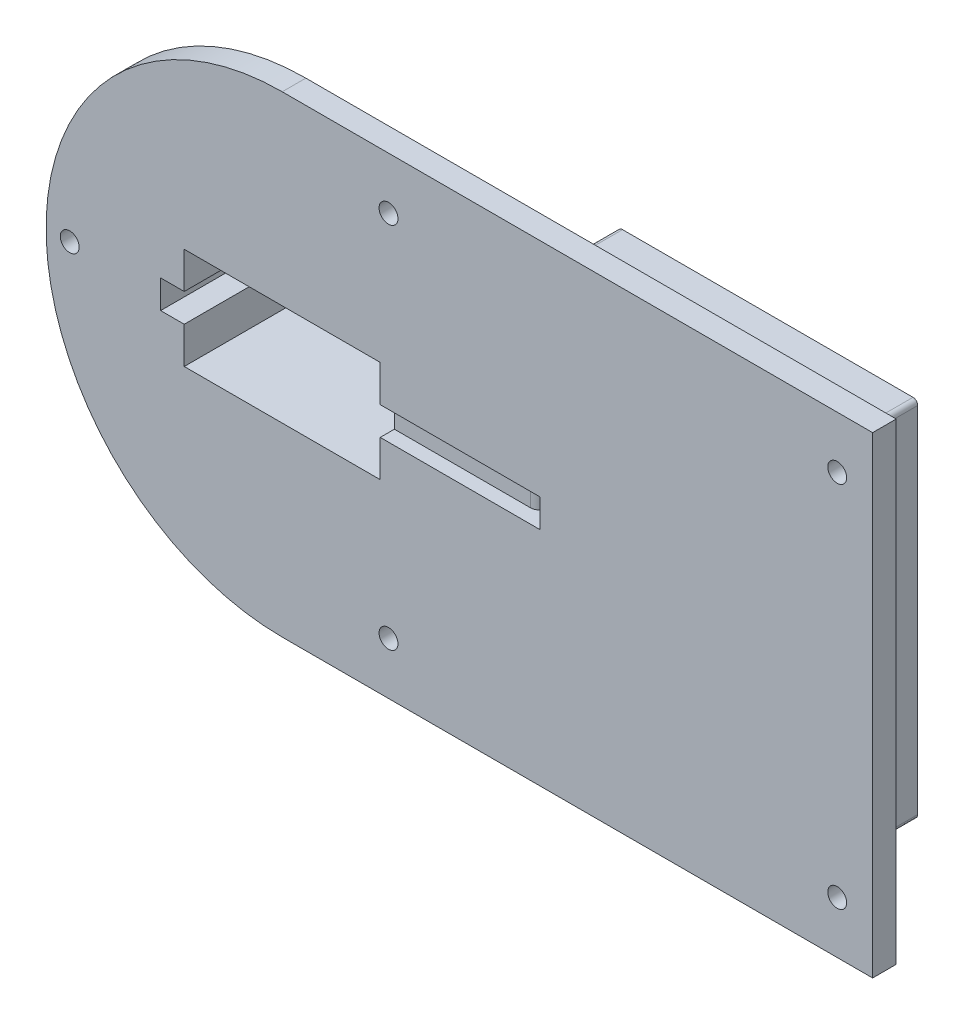
SolidWorks part; units mm, degrees
ref_plane "Front Plane" through (0, 0, 0) normal (0, 0, 1) x (1, 0, 0)
ref_plane "Top Plane" through (0, 0, 0) normal (0, 1, 0) x (1, 0, 0)
ref_plane "Right Plane" through (0, 0, 0) normal (1, 0, 0) x (0, 0, -1)
sketch "Sketch1" plane through (0, 0, 0) normal (0, 0, 1) x (1, 0, 0)
  line L1 (-20.75, 10.75) -> (20.75, 10.75)
  line L2 (-20.75, 10.75) -> (-20.75, -10.75)
  line L3 (-20.75, -10.75) -> (20.75, -10.75)
  line L4 (20.75, 10.75) -> (20.75, -10.75)
  line L5 (-20.75, 10.75) -> (20.75, -10.75) construction
  line L6 (-20.75, -10.75) -> (20.75, 10.75) construction
  line L11 (30, 15) -> (-30, 15)
  line L12 (30, 15) -> (30, -15)
  line L13 (30, -15) -> (-30, -15)
  line L14 (-30, 15) -> (-30, -15)
  line L15 (30, 15) -> (-30, -15) construction
  line L16 (30, -15) -> (-30, 15) construction
  point P0 (0, 0)
  point P6 (0, 0)
extrude "Boss-Extrude1" add sketch "Sketch1" along normal blind 27
sketch "Sketch2" plane through (0, 0, 27) normal (0, 0, 1) x (1, 0, 0)
  circle A0 centre (0, 0) radius 50
extrude "Boss-Extrude2" add sketch "Sketch2" along normal blind 5
fillet "Fillet2" radius 10 4 edges at (-30, 0, 27) (30, 0, 27) (0, 15, 27) (0, -15, 27)
sketch "Sketch6" plane through (0, 0, 0) normal (0, 0, -1) x (-1, 0, 0)
  line L0 (30, 5.975) -> (24.4, 5.975) construction
  line L1 (30, -15) -> (30, 15) construction
  line L2 (24.4, 15) -> (24.4, 5) construction
  line L3 (30, 15) -> (-30, 15) construction
  line L4 (0, 0) -> (11.2305, 0) construction
  line L5 (0, 0) -> (0, 9.663) construction
  circle A0 centre (24.4, 5) radius 1
  circle A1 centre (-24.4, 5) radius 1
  circle A2 centre (24.4, -5) radius 1
  circle A3 centre (-24.4, -5) radius 1
extrude "Cut-Extrude2" cut sketch "Sketch6" against normal blind 15
sketch "Sketch7" plane through (0, 0, 0) normal (0, 0, -1) x (-1, 0, 0)
  line L1 (-20.75, 10.75) -> (20.75, 10.75)
  line L2 (-20.75, 10.75) -> (-20.75, -10.75)
  line L3 (-20.75, -10.75) -> (20.75, -10.75)
  line L4 (20.75, 10.75) -> (20.75, -10.75)
  line L5 (-20.75, 10.75) -> (20.75, -10.75) construction
  line L6 (-20.75, -10.75) -> (20.75, 10.75) construction
  point P0 (0, 0)
extrude "Cut-Extrude3" cut sketch "Sketch7" against normal blind 69
sketch "Sketch8" plane through (0, 0, 0) normal (0, 0, -1) x (-1, 0, 0)
  line L0 (20.75, 10.75) -> (20.75, -10.75) construction
  line L1 (15.75, 3) -> (25.75, 3)
  line L2 (15.75, 3) -> (15.75, -3)
  line L3 (15.75, -3) -> (25.75, -3)
  line L4 (25.75, 3) -> (25.75, -3)
  line L5 (15.75, 3) -> (25.75, -3) construction
  line L6 (15.75, -3) -> (25.75, 3) construction
  point P0 (20.75, 0)
extrude "Cut-Extrude4" cut sketch "Sketch8" against normal blind 75
sketch "Sketch10" plane through (0, 0, 32) normal (0, 0, 1) x (1, 0, 0)
  line L0 (-25.75, 3) -> (-25.75, -3) construction
  line L1 (0, 3) -> (74.5949, 3)
  line L3 (0, -3) -> (74.5949, -3)
  line L4 (74.5949, 3) -> (74.5949, -3)
  line L5 (0, -0.7698) -> (74.5949, -3) construction
  line L6 (0, 0.7698) -> (74.5949, 3) construction
  line L7 (0, 3) -> (0, -3)
  point P0 (-25.75, 0)
extrude "Cut-Extrude5" cut sketch "Sketch10" against normal blind 3
sketch "Sketch11" plane through (0, 0, 27) normal (0, 0, -1) x (-1, 0, 0)
  line L0 (0, 0) -> (-45, 0) construction
  line L1 (0, 0) -> (45, 0) construction
  line L2 (0, 0) -> (-22.5, -38.9711) construction
  line L3 (0, 0) -> (-22.5, 38.9711) construction
  circle A3 centre (45, 0) radius 2
  circle A4 centre (-22.5, 38.9711) radius 2
  circle A5 centre (-22.5, -38.9711) radius 2
extrude "Cut-Extrude6" cut sketch "Sketch11" against normal blind 16
sketch "Sketch12" plane through (0, 0, 27) normal (0, 0, -1) x (-1, 0, 0)
  line L1 (0, -50) -> (-125, -50)
  line L3 (0, 50) -> (-125, 50)
  line L4 (-125, -50) -> (-125, 50)
  line L5 (-46.4238, 18.5695) -> (-125, 50) construction
  line L6 (-46.4238, -18.5695) -> (-125, -50) construction
  arc A0 (0, 50) -> (0, -50) centre (0, 0) ccw
  point P0 (0, 0)
extrude "Boss-Extrude3" add sketch "Sketch12" against normal up to surface (5 mm away) up to face at (-43, 0, 32)
sketch "Sketch13" plane through (0, 0, 27) normal (0, 0, -1) x (-1, 0, 0)
  line L0 (-99.6294, -50) -> (-99.6294, -20) construction
  line L1 (-125, -50) -> (0, -50) construction
  line L2 (-125, -20) -> (-104.5, -20) construction
  line L3 (-125, 50) -> (-125, -50) construction
  circle A0 centre (-104.5, -20) radius 1
  circle A1 centre (-104.5, -20) radius 2.5
extrude "Boss-Extrude4" add sketch "Sketch13" along normal blind 4
sketch "Sketch14" plane through (0, 0, 27) normal (0, 0, -1) x (-1, 0, 0)
  line L0 (-125, -12.166) -> (-56.25, -12.166) construction
  line L1 (-125, 50) -> (-125, -50) construction
  line L2 (-56.25, -50) -> (-56.25, -21.25) construction
  line L3 (-125, -50) -> (0, -50) construction
  circle A0 centre (-56.25, -21.25) radius 1
  circle A1 centre (-56.25, -21.25) radius 2.5
extrude "Boss-Extrude5" add sketch "Sketch14" along normal blind 4
sketch "Sketch15" plane through (0, 0, 27) normal (0, 0, -1) x (-1, 0, 0)
  line L0 (-56.8712, -50) -> (-56.8712, 30.85) construction
  line L1 (-125, -50) -> (0, -50) construction
  line L2 (-125, 30.85) -> (-61.34, 30.85) construction
  line L3 (-125, 50) -> (-125, -50) construction
  line L4 (-125, 30.85) -> (-89.2, 30.85) construction
  circle A0 centre (-61.34, 30.85) radius 1
  circle A1 centre (-61.34, 30.85) radius 2.5
  circle A2 centre (-89.2, 30.85) radius 1
  circle A3 centre (-89.2, 30.85) radius 2.5
extrude "Boss-Extrude6" add sketch "Sketch15" along normal blind 4
sketch "Sketch16" plane through (0, 0, 27) normal (0, 0, -1) x (-1, 0, 0)
  line L0 (-76.0061, -50) -> (-76.0061, -35.75) construction
  line L1 (-125, -50) -> (0, -50) construction
  line L2 (-76.0061, -35.75) -> (-76.0061, 35.25) construction
  line L3 (-125, 7.2051) -> (-109.05, 7.2051) construction
  line L4 (-125, 50) -> (-125, -50) construction
  line L5 (-109.05, 7.2051) -> (-109.05, 35.25)
  line L6 (-109.05, 35.25) -> (-51.55, 35.25)
  line L7 (-51.55, 35.25) -> (-51.55, -35.75)
  line L8 (-51.55, -35.75) -> (-109.05, -35.75)
  line L9 (-109.05, -35.75) -> (-109.05, 7.2051)
  line L10 (-112.05, 38.25) -> (-48.55, 38.25)
  line L11 (-48.55, 38.25) -> (-48.55, -38.75)
  line L12 (-48.55, -38.75) -> (-112.05, -38.75)
  line L13 (-112.05, -38.75) -> (-112.05, 7.2051)
  line L14 (-112.05, 7.2051) -> (-112.05, 38.25)
  dimension "D1" = 3
extrude "Boss-Extrude8" add sketch "Sketch16" along normal blind 17.5
sketch "Sketch17" plane through (0, 0, 27) normal (0, 0, -1) x (-1, 0, 0)
  line L0 (0, 0) -> (-51.55, 0) construction
  line L1 (-51.55, -35.75) -> (-51.55, 35.25) construction
  line L2 (-51.55, 3) -> (-51.55, -3)
  line L3 (-51.55, -3) -> (-54.55, -3)
  line L4 (-54.55, -3) -> (-54.55, 3)
  line L5 (-54.55, 3) -> (-51.55, 3)
  point P8 (-51.55, 0)
extrude "Cut-Extrude7" cut sketch "Sketch17" against normal blind 17.5
sketch "Sketch18" plane through (0, 0, 32) normal (0, 0, 1) x (1, 0, 0)
  line L0 (49.9099, 3) -> (51.55, 3)
  line L1 (51.55, 3) -> (51.55, -3)
  line L2 (51.55, -3) -> (49.9099, -3)
  line L3 (49.9099, -3) -> (49.9099, 3)
extrude "Cut-Extrude8" cut sketch "Sketch18" against normal up to surface (3 mm away) up to face at (35.3525, 0, 29)
sketch "Sketch20" plane through (0, 0, 23) normal (0, 0, -1) x (-1, 0, 0)
  line L0 (-125, -50) -> (-98.25, -50) construction
  line L1 (-125, -50) -> (0, -50) construction
  line L2 (-98.25, -50) -> (-98.25, -27.9937) construction
  line L3 (-98.25, -27.9937) -> (-85.25, -27.9937) construction
  line L4 (-98.25, -27.9937) -> (-85.25, -27.9937)
  line L5 (-85.25, -27.9937) -> (-85.25, -43.8213)
  line L6 (-85.25, -43.8213) -> (-98.25, -43.8213)
  line L7 (-98.25, -43.8213) -> (-98.25, -27.9937)
extrude "Cut-Extrude9" cut sketch "Sketch20" along normal blind 25
sketch "Sketch21" plane through (0, 0, 9.5) normal (0, 0, -1) x (-1, 0, 0)
  line L0 (-85.25, -35.75) -> (-66.43, -35.75)
  line L1 (-109.05, -35.75) -> (-51.55, -35.75) construction
  line L2 (-66.43, -35.75) -> (-66.43, -38.75)
  line L3 (-112.05, -38.75) -> (-48.55, -38.75) construction
  line L4 (-66.43, -38.75) -> (-56.43, -38.75)
  line L5 (-56.43, -38.75) -> (-56.43, -35.75)
  line L6 (-85.25, -35.75) -> (-51.55, -35.75) construction
  line L7 (-56.43, -35.75) -> (-66.43, -35.75)
extrude "Cut-Extrude10" cut sketch "Sketch21" against normal up to surface (13.5 mm away) contours L2 L4 L5 L7 up to face at (91.75, -37.25, 23)
sketch "Sketch23" plane through (0, 0, 23) normal (0, 0, -1) x (-1, 0, 0)
  line L0 (-98.25, -35.75) -> (-85.25, -35.75)
  line L1 (-85.25, -35.75) -> (-85.25, -38.75)
  line L2 (-85.25, -38.75) -> (-98.25, -38.75)
  line L3 (-98.25, -38.75) -> (-98.25, -35.75)
  line L4 (-66.43, -35.75) -> (-56.43, -35.75)
  line L5 (-56.43, -35.75) -> (-56.43, -38.75)
  line L6 (-56.43, -38.75) -> (-66.43, -38.75)
  line L7 (-66.43, -38.75) -> (-66.43, -35.75)
extrude "Boss-Extrude9" add sketch "Sketch23" along normal blind 1.75
fillet "Fillet3" radius 1 4 edges at (112.05, 38.25, 18.25) (48.55, 38.25, 18.25) (48.55, -38.75, 18.25) (112.05, -38.75, 18.25)
sketch "Sketch24" plane through (0, 0, 27) normal (0, 0, -1) x (-1, 0, 0)
  line L0 (-22.5, 38.9711) -> (-117.5, 38.9711) construction
  line L1 (-117.5, 38.9711) -> (-117.5, -38.9711) construction
  line L2 (-117.5, -38.9711) -> (-22.5, -38.9711) construction
  circle A0 centre (-117.5, 38.9711) radius 2
  circle A1 centre (-117.5, -38.9711) radius 2
extrude "Cut-Extrude11" cut sketch "Sketch24" against normal blind 17
sketch "Sketch25" plane through (0, 0, 0) normal (0, 0, -1) x (-1, 0, 0)
  line L0 (25.75, -3) -> (25.75, 3) construction
  line L1 (20.3887, 3) -> (31.1113, 3)
  line L2 (20.3887, 3) -> (20.3887, -3)
  line L3 (20.3887, -3) -> (31.1113, -3)
  line L4 (31.1113, 3) -> (31.1113, -3)
  line L5 (20.3887, 3) -> (31.1113, -3) construction
  line L6 (20.3887, -3) -> (31.1113, 3) construction
  point P0 (25.75, 0)
extrude "Cut-Extrude12" cut sketch "Sketch25" against normal blind 3
fillet "Fillet4" radius 2 2 edges at (-25.75, 0, 3) (51.55, 0, 29)
